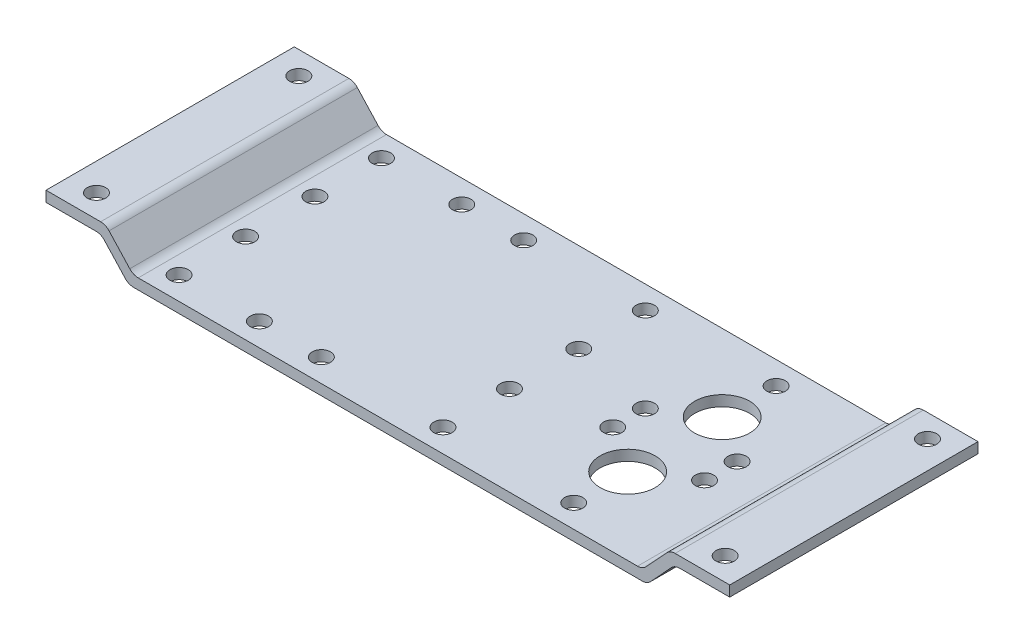
SolidWorks part; units mm, degrees
material "AISI 1020"
ref_plane "Plan de face" through (0, 0, 0) normal (0, 0, 1) x (1, 0, 0)
ref_plane "Plan de dessus" through (0, 0, 0) normal (0, 1, 0) x (1, 0, 0)
ref_plane "Plan de droite" through (0, 0, 0) normal (1, 0, 0) x (0, 0, -1)
sketch "Esquisse1" plane through (0, 0, 0) normal (0, 0, 1) x (1, 0, 0)
  line L0 (0, 0) -> (11.9054, 0)
  line L1 (13.7424, -0.8043) -> (18.2576, -5.6957)
  line L2 (20.0946, -6.5) -> (128.9054, -6.5)
  line L3 (0, -2.3) -> (10.8984, -2.3)
  line L4 (12.7354, -3.1043) -> (17.2506, -7.9957)
  line L5 (19.0876, -8.8) -> (129.9124, -8.8)
  line L6 (0, -2.3) -> (0, 0)
  line L7 (74.5, -8.8) -> (74.5, -6.5) construction
  line L8 (11.993, -2.3) -> (17.993, -8.8) construction
  line L9 (17.993, -8.8) -> (74.5, -8.8) construction
  line L10 (13, 0) -> (19, -6.5) construction
  line L11 (19, -6.5) -> (74.5, -6.5) construction
  line L12 (0, -2.3) -> (11.993, -2.3) construction
  line L13 (0, 0) -> (13, 0) construction
  line L14 (149, -2.3) -> (149, 0)
  line L15 (136.2646, -3.1043) -> (131.7494, -7.9957)
  line L16 (149, -2.3) -> (138.1016, -2.3)
  line L17 (135.2576, -0.8043) -> (130.7424, -5.6957)
  line L18 (149, 0) -> (137.0946, 0)
  arc A0 (17.2506, -7.9957) -> (19.0876, -8.8) centre (19.0876, -6.3) ccw
  arc A1 (18.2576, -5.6957) -> (20.0946, -6.5) centre (20.0946, -4) ccw
  arc A2 (10.8984, -2.3) -> (12.7354, -3.1043) centre (10.8984, -4.8) cw
  arc A3 (11.9054, 0) -> (13.7424, -0.8043) centre (11.9054, -2.5) cw
  arc A4 (137.0946, 0) -> (135.2576, -0.8043) centre (137.0946, -2.5) ccw
  arc A5 (138.1016, -2.3) -> (136.2646, -3.1043) centre (138.1016, -4.8) ccw
  arc A6 (130.7424, -5.6957) -> (128.9054, -6.5) centre (128.9054, -4) cw
  arc A7 (131.7494, -7.9957) -> (129.9124, -8.8) centre (129.9124, -6.3) cw
  point P15 (19, -6.5)
  point P22 (0, 0)
  point P37 (130, -6.5)
  dimension "D6" = 2.5
  dimension "D1" = 74.5
  dimension "D2" = 9.1962
  dimension "D3" = 4
  dimension "D4" = 19
  dimension "D5" = 2.3
extrude "Boss.-Extru.1" add sketch "Esquisse1" along normal blind 54.1
sketch "Esquisse2" plane through (0, 0, 0) normal (0, 1, 0) x (1, 0, 0)
  line L0 (149, -54.1) -> (149, 0) construction
  line L1 (0, -54.1) -> (0, 0) construction
  line L2 (11.9054, 0) -> (0, 0) construction
  line L3 (0, -27.05) -> (149, -27.05) construction
  line L4 (128.9054, 0) -> (20.0946, 0) construction
  circle A0 centre (6, -5) radius 2
  circle A1 centre (24, -5) radius 2
  circle A2 centre (41.5, -5) radius 2
  circle A3 centre (55, -5) radius 2
  circle A4 centre (81.5, -5) radius 2
  circle A5 centre (110, -5) radius 2
  circle A6 centre (143, -5) radius 2
  circle A7 centre (120, -30.6) radius 2
  circle A8 centre (100, -30.6) radius 2
  circle A9 centre (110, -37.35) radius 6
  circle A10 centre (81.5, -34.6) radius 2
  circle A11 centre (24, -34.6) radius 2
  circle A12 centre (143, -49.1) radius 2
  circle A13 centre (110, -49.1) radius 2
  circle A14 centre (24, -19.5) radius 2
  circle A15 centre (81.5, -19.5) radius 2
  circle A16 centre (110, -16.75) radius 6
  circle A17 centre (120, -23.5) radius 2
  circle A18 centre (100, -23.5) radius 2
  circle A19 centre (81.5, -49.1) radius 2
  circle A20 centre (55, -49.1) radius 2
  circle A21 centre (41.5, -49.1) radius 2
  circle A22 centre (24, -49.1) radius 2
  circle A23 centre (6, -49.1) radius 2
  dimension "D1" = 4
  dimension "D12" = 12
  dimension "D2" = 18
  dimension "D3" = 17.5
  dimension "D4" = 13.5
  dimension "D5" = 26.5
  dimension "D6" = 28.5
  dimension "D7" = 6
  dimension "D8" = 6
  dimension "D9" = 5
  dimension "D10" = 14.5
  dimension "D11" = 16.75
  dimension "D13" = 23.5
  dimension "D14" = 29
  dimension "D15" = 10
extrude "Enlèv. mat.-Extru.1" cut sketch "Esquisse2" against normal through all
